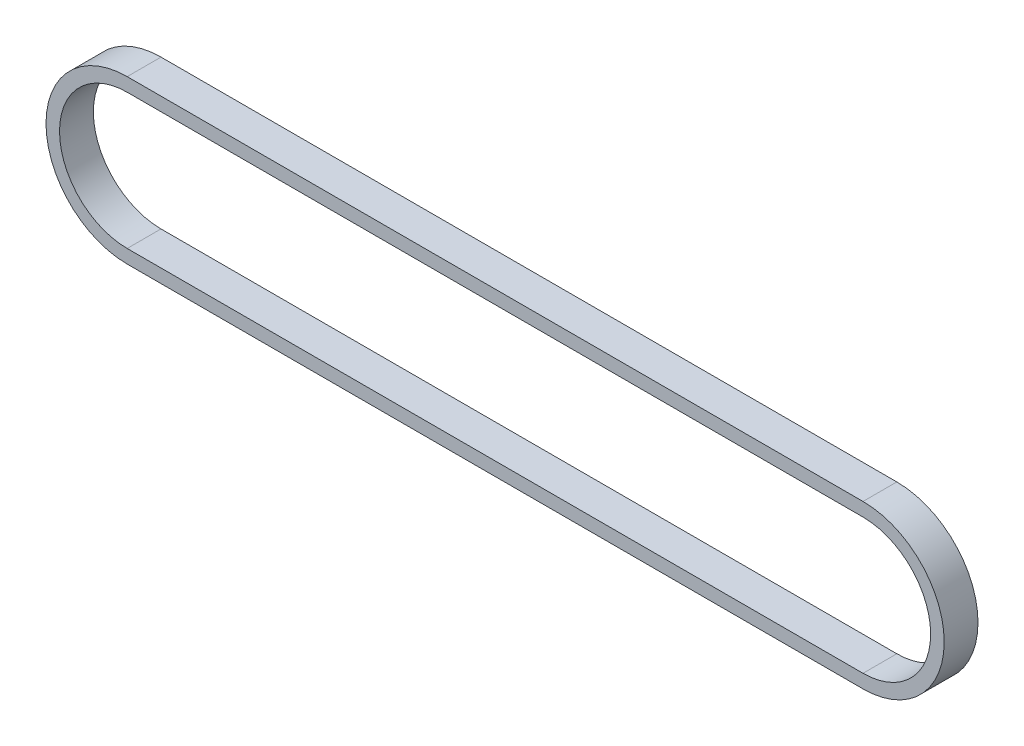
SolidWorks part; units mm, degrees
ref_plane "Front Plane" through (0, 0, 0) normal (0, 0, 1) x (1, 0, 0)
ref_plane "Top Plane" through (0, 0, 0) normal (0, 1, 0) x (1, 0, 0)
ref_plane "Right Plane" through (0, 0, 0) normal (1, 0, 0) x (0, 0, -1)
sketch "Sketch1" plane through (0, 0, 0) normal (0, 0, 1) x (1, 0, 0)
  line L0 (0, 0) -> (138.1511, 0) construction
  line L1 (0, 12.7) -> (138.1511, 12.7)
  line L2 (0, -12.7) -> (138.1511, -12.7)
  line L3 (0, 15.24) -> (138.1511, 15.24)
  line L4 (0, -15.24) -> (138.1511, -15.24)
  arc A0 (0, 12.7) -> (0, -12.7) centre (0, 0) ccw
  arc A1 (138.1511, -12.7) -> (138.1511, 12.7) centre (138.1511, 0) ccw
  arc A2 (138.1511, -15.24) -> (138.1511, 15.24) centre (138.1511, 0) ccw
  arc A3 (0, 15.24) -> (0, -15.24) centre (0, 0) ccw
  point P3 (69.0756, 0)
  dimension "D3" = 12.7
  dimension "D2" = 138.1511
  dimension "D1" = 2.54
extrude "Boss-Extrude1" add sketch "Sketch1" along normal blind 6.35
